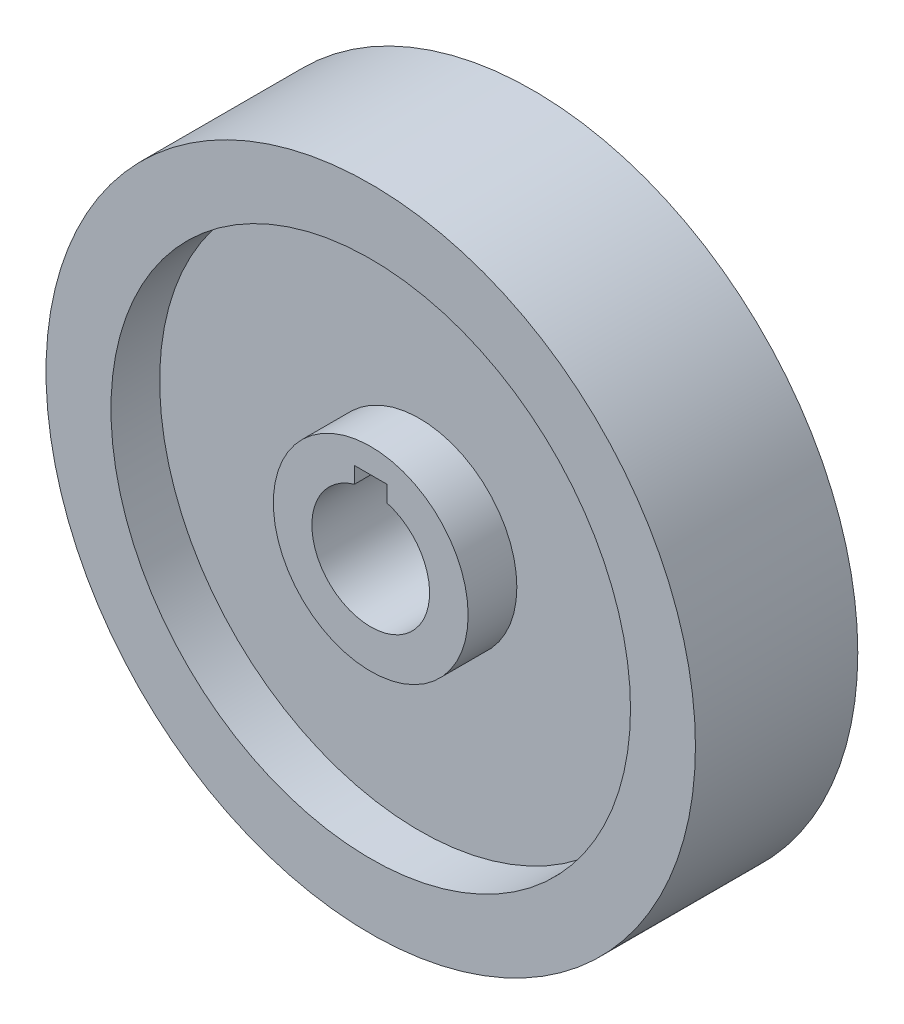
SolidWorks part; units mm, degrees
ref_plane "Front Plane" through (0, 0, 0) normal (0, 0, 1) x (1, 0, 0)
ref_plane "Top Plane" through (0, 0, 0) normal (0, 1, 0) x (1, 0, 0)
ref_plane "Right Plane" through (0, 0, 0) normal (1, 0, 0) x (0, 0, -1)
sketch "Sketch1" plane through (0, 0, 0) normal (1, 0, 0) x (0, 0, -1)
  line L0 (-34.2145, 0) -> (34.2145, 0) construction
  line L1 (0, 0) -> (0, 63.5) construction
  line L2 (15.875, 11.5094) -> (-15.875, 11.5094)
  line L3 (-15.875, 11.5094) -> (-15.875, 19.05)
  line L4 (-15.875, 19.05) -> (-6.35, 19.05)
  line L5 (-6.35, 19.05) -> (-6.35, 50.8)
  line L6 (-6.35, 50.8) -> (-15.875, 50.8)
  line L7 (-15.875, 50.8) -> (-15.875, 63.5)
  line L8 (-15.875, 63.5) -> (15.875, 63.5)
  line L9 (15.875, 11.5094) -> (15.875, 19.05)
  line L10 (15.875, 19.05) -> (6.35, 19.05)
  line L11 (6.35, 19.05) -> (6.35, 50.8)
  line L12 (6.35, 50.8) -> (15.875, 50.8)
  line L13 (15.875, 50.8) -> (15.875, 63.5)
  point P13 (0, 11.5094)
  dimension "D1" = 31.75
  dimension "D2" = 127
  dimension "D3" = 23.0188
  dimension "D4" = 12.7
  dimension "D5" = 38.1
  dimension "D6" = 12.7
revolve "Revolve1" add sketch "Sketch1" angle 360 about L0
sketch "Sketch4" plane through (0, 0, -15.875) normal (0, 0, -1) x (-1, 0, 0)
  line L0 (-3.175, 11.0628) -> (3.175, 11.0628)
  line L1 (3.175, 11.0628) -> (3.175, 14.2378)
  line L2 (3.175, 14.2378) -> (-3.175, 14.2378)
  line L3 (-3.175, 14.2378) -> (-3.175, 11.0628)
  circle A0 centre (0, 0) radius 11.5094 construction
  dimension "D1" = 6.35
  dimension "D2" = 3.175
extrude "Cut-Extrude1" cut sketch "Sketch4" against normal through all
